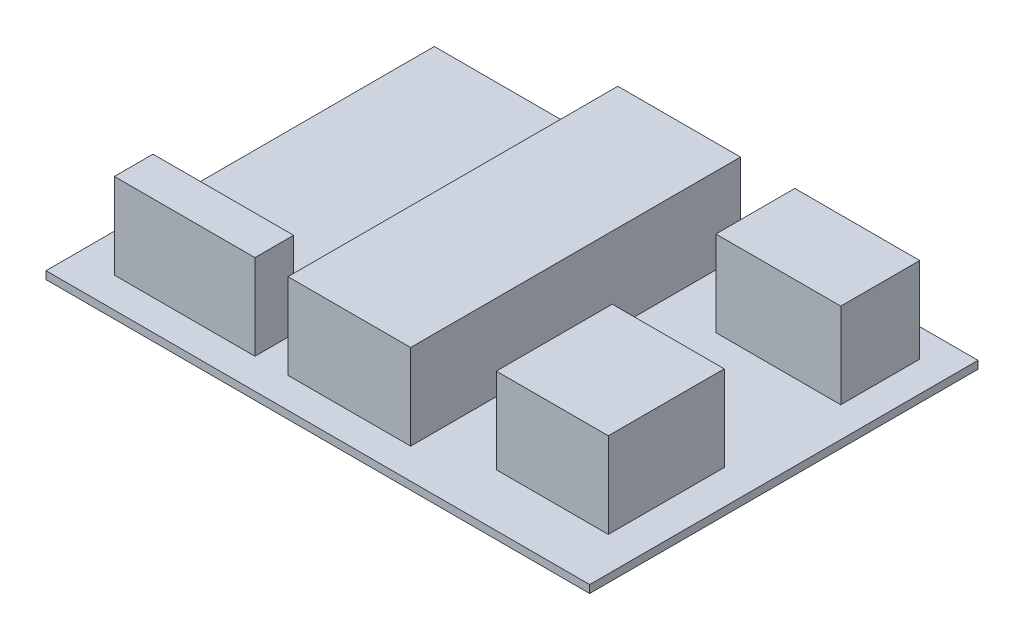
SolidWorks part; units mm, degrees
ref_plane "Front Plane" through (0, 0, 0) normal (0, 0, 1) x (1, 0, 0)
ref_plane "Top Plane" through (0, 0, 0) normal (0, 1, 0) x (1, 0, 0)
ref_plane "Right Plane" through (0, 0, 0) normal (1, 0, 0) x (0, 0, -1)
sketch "Sketch1" plane through (0, 0, 0) normal (0, 1, 0) x (1, 0, 0)
  line L1 (-31.8106, 37.6619) -> (38.1894, 37.6619)
  line L2 (-31.8106, 37.6619) -> (-31.8106, -12.3381)
  line L3 (-31.8106, -12.3381) -> (38.1894, -12.3381)
  line L4 (38.1894, 37.6619) -> (38.1894, -12.3381)
  dimension "D1" = 70
  dimension "D2" = 50
extrude "Boss-Extrude1" add sketch "Sketch1" along normal blind 1
sketch "Sketch2" plane through (0, 0, 0) normal (0, 1, 0) x (1, 0, 0)
  line L1 (-4.5623, 34.0424) -> (11.2297, 34.0424)
  line L2 (-4.5623, 34.0424) -> (-4.5623, -8.4302)
  line L3 (-4.5623, -8.4302) -> (11.2297, -8.4302)
  line L4 (11.2297, 34.0424) -> (11.2297, -8.4302)
  line L5 (18.2243, 34.0424) -> (34.3048, 34.0424)
  line L6 (18.2243, 34.0424) -> (18.2243, 23.8749)
  line L7 (18.2243, 23.8749) -> (34.3048, 23.8749)
  line L8 (34.3048, 34.0424) -> (34.3048, 23.8749)
  line L9 (19.3781, 9.3809) -> (33.8, 9.3809)
  line L10 (19.3781, 9.3809) -> (19.3781, -5.5458)
  line L11 (19.3781, -5.5458) -> (33.8, -5.5458)
  line L12 (33.8, 9.3809) -> (33.8, -5.5458)
  line L13 (-26.9163, -8.4302) -> (-8.8168, -8.4302)
  line L14 (-26.9163, -8.4302) -> (-26.9163, -3.4546)
  line L15 (-26.9163, -3.4546) -> (-8.8168, -3.4546)
  line L16 (-8.8168, -8.4302) -> (-8.8168, -3.4546)
extrude "Boss-Extrude2" add sketch "Sketch2" along normal blind 12
